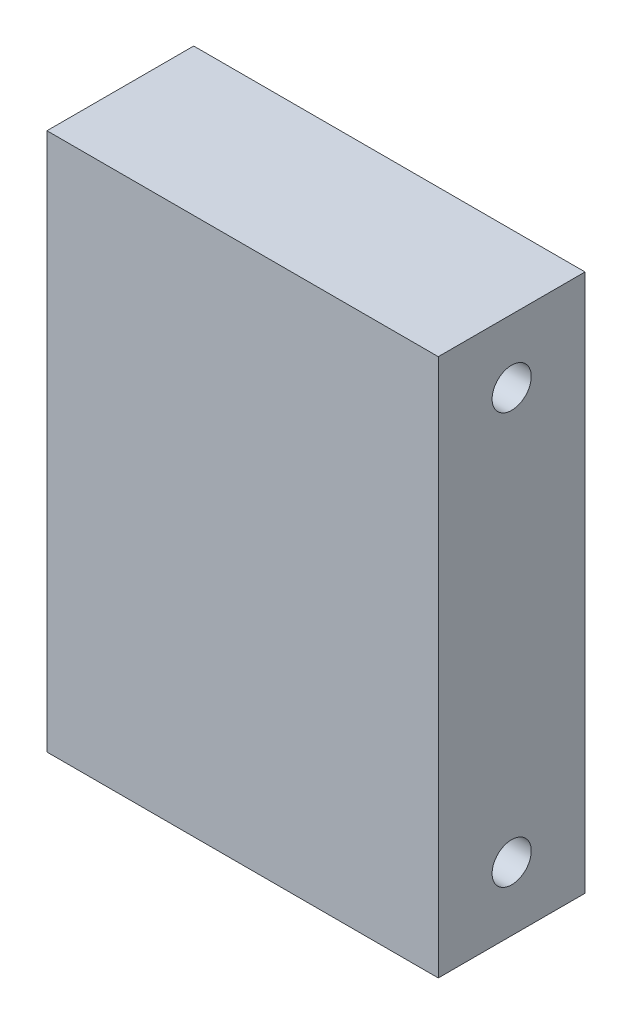
SolidWorks part; units mm, degrees
ref_plane "Plan de face" through (0, 0, 0) normal (0, 0, 1) x (1, 0, 0)
ref_plane "Plan de dessus" through (0, 0, 0) normal (0, 1, 0) x (1, 0, 0)
ref_plane "Plan de droite" through (0, 0, 0) normal (1, 0, 0) x (0, 0, -1)
sketch "Esquisse1" plane through (0, 0, 0) normal (0, 0, 1) x (1, 0, 0)
  line L1 (-20, 27.5) -> (20, 27.5)
  line L2 (-20, 27.5) -> (-20, -27.5)
  line L3 (-20, -27.5) -> (20, -27.5)
  line L4 (20, 27.5) -> (20, -27.5)
  point P7 (-3.9479, -9.2584)
  dimension "D1" = 55
  dimension "D2" = 40
  dimension "D3" = 20
  dimension "D4" = 27.5
extrude "Boss.-Extru.1" add sketch "Esquisse1" along normal blind 15
sketch "Esquisse2" plane through (20, 0, 0) normal (1, 0, 0) x (0, 0, -1)
  line L0 (-15, -27.5) -> (0, -27.5) construction
  line L3 (-7.5, 21) -> (-7.5, -21) construction
  line L4 (-15, -27.5) -> (-15, 27.5) construction
  circle A0 centre (-7.5, 21) radius 2
  circle A1 centre (-7.5, -21) radius 2
  dimension "D1" = 4
  dimension "D2" = 4
  dimension "D4" = 6.5
  dimension "D3" = 42
  dimension "D5" = 7.5
extrude "Enlèv. mat.-Extru.1" cut sketch "Esquisse2" against normal blind 5
sketch "Esquisse3" plane through (-20, 0, 0) normal (-1, 0, 0) x (0, 0, 1)
  line L0 (15, -27.5) -> (0, -27.5) construction
  line L2 (7.5, 21) -> (7.5, -21) construction
  line L3 (0, 27.5) -> (0, -27.5) construction
  circle A0 centre (7.5, 21) radius 2
  circle A1 centre (7.5, -21) radius 2
  point P4 (7.5, -27.5)
  dimension "D1" = 4
  dimension "D2" = 4
  dimension "D4" = 6.5
  dimension "D3" = 42
  dimension "D5" = 7.5
extrude "Enlèv. mat.-Extru.2" cut sketch "Esquisse3" against normal blind 5
equation "\"D3@Esquisse1\"=\"D2@Esquisse1\"/2"
equation "\"D4@Esquisse1\"=\"D1@Esquisse1\"/2"
